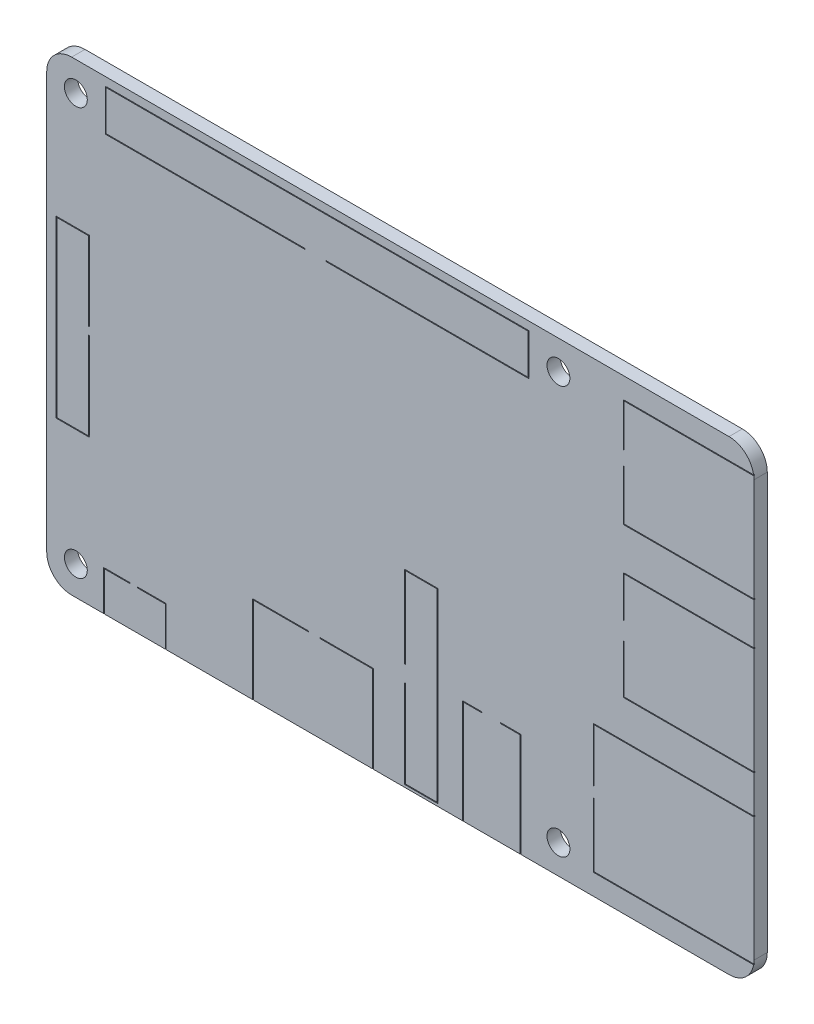
SolidWorks part; units mm, degrees
ref_plane "Front Plane" through (0, 0, 0) normal (0, 0, 1) x (1, 0, 0)
ref_plane "Top Plane" through (0, 0, 0) normal (0, 1, 0) x (1, 0, 0)
ref_plane "Right Plane" through (0, 0, 0) normal (1, 0, 0) x (0, 0, -1)
sketch "Sketch1" plane through (0, 0, 0) normal (0, 0, 1) x (1, 0, 0)
  line L1 (-39.5, -28) -> (39.5, -28)
  line L2 (-42.5, -25) -> (-42.5, 25)
  line L3 (-39.5, 28) -> (39.5, 28)
  line L4 (42.5, -25) -> (42.5, 25)
  line L5 (-42.5, -28) -> (42.5, 28) construction
  line L6 (-42.5, 28) -> (42.5, -28) construction
  arc A0 (-39.5, -28) -> (-42.5, -25) centre (-39.5, -25) cw
  arc A1 (39.5, -28) -> (42.5, -25) centre (39.5, -25) ccw
  arc A2 (39.5, 28) -> (42.5, 25) centre (39.5, 25) cw
  arc A3 (-42.5, 25) -> (-39.5, 28) centre (-39.5, 25) cw
  circle A4 centre (-39, 24.5) radius 1.375
  circle A5 centre (-39, -24.5) radius 1.375
  circle A6 centre (19, 24.5) radius 1.375
  circle A7 centre (19, -24.5) radius 1.375
  point P0 (0, 0)
  dimension "D3" = 3
  dimension "D4" = 2.75
  dimension "D5" = 3.5
  dimension "D6" = 3.5
  dimension "D7" = 58
  dimension "D8" = 58
  dimension "D9" = 49
  dimension "D12" = 49
  dimension "D1" = 85
  dimension "D2" = 56
  dimension "D10" = 24.5
  dimension "D11" = 24.5
extrude "Boss-Extrude1" add sketch "Sketch1" along normal blind 1.6
sketch "Sketch2" plane through (0, 0, 1.6) normal (0, 0, 1) x (1, 0, 0)
  line L1 (-42.5, 25) -> (-42.5, -25) construction
  line L2 (-35.65, -28.6369) -> (-28.15, -28.6369)
  line L3 (-35.65, -28.6369) -> (-35.65, -23.2)
  line L4 (-35.65, -23.2) -> (-32.465, -23.2)
  line L5 (-28.15, -28.6369) -> (-28.15, -23.2)
  line L6 (-35.65, -28.6369) -> (-28.15, -23.2) construction
  line L7 (-35.65, -23.2) -> (-28.15, -28.6369) construction
  line L8 (-39.5, -28) -> (39.5, -28) construction
  line L9 (-17.75, -17.5) -> (-11.0158, -17.5)
  line L10 (-17.75, -17.5) -> (-17.75, -33.1614)
  line L11 (-17.75, -33.1614) -> (-3.25, -33.1614)
  line L12 (-3.25, -17.5) -> (-3.25, -33.1614)
  line L13 (-17.75, -17.5) -> (-3.25, -33.1614) construction
  line L14 (-17.75, -33.1614) -> (-3.25, -17.5) construction
  line L15 (0.5, -5.3) -> (4.5, -5.3)
  line L16 (0.5, -5.3) -> (0.5, -15.174)
  line L17 (0.5, -27.7) -> (4.5, -27.7)
  line L18 (4.5, -5.3) -> (4.5, -27.7)
  line L19 (0.5, -5.3) -> (4.5, -27.7) construction
  line L20 (0.5, -27.7) -> (4.5, -5.3) construction
  line L21 (7.5, -15.5) -> (9.7992, -15.5)
  line L22 (7.5, -15.5) -> (7.5, -31.1614)
  line L23 (7.5, -31.1614) -> (14.5, -31.1614)
  line L24 (14.5, -15.5) -> (14.5, -31.1614)
  line L25 (7.5, -15.5) -> (14.5, -31.1614) construction
  line L26 (7.5, -31.1614) -> (14.5, -15.5) construction
  line L27 (-35.45, 27) -> (15.45, 27)
  line L28 (-35.45, 27) -> (-35.45, 22)
  line L29 (-35.45, 22) -> (-11.4582, 22)
  line L30 (15.45, 27) -> (15.45, 22)
  line L31 (-35.45, 27) -> (15.45, 22) construction
  line L32 (-35.45, 22) -> (15.45, 27) construction
  line L33 (-41.3717, -10.5142) -> (-37.3717, -10.5142)
  line L34 (-41.3717, -10.5142) -> (-41.3717, 10.5142)
  line L35 (-41.3717, 10.5142) -> (-37.3717, 10.5142)
  line L36 (-37.3717, -10.5142) -> (-37.3717, 0.0947)
  line L37 (-41.3717, -10.5142) -> (-37.3717, 10.5142) construction
  line L38 (-41.3717, 10.5142) -> (-37.3717, -10.5142) construction
  line L39 (42.5, -25) -> (42.5, 25) construction
  line L40 (23.2, -25.5) -> (44.7, -25.5)
  line L41 (23.2, -25.5) -> (23.2, -17.75)
  line L42 (23.2, -10) -> (44.7, -10)
  line L43 (44.7, -25.5) -> (44.7, -10)
  line L44 (23.2, -25.5) -> (44.7, -10) construction
  line L45 (23.2, -10) -> (44.7, -25.5) construction
  line L46 (26.8, -5.5) -> (54.0714, -5.5)
  line L47 (26.8, -5.5) -> (26.8, 0.4072)
  line L48 (26.8, 7.5) -> (54.0714, 7.5)
  line L49 (54.0714, -5.5) -> (54.0714, 7.5)
  line L50 (26.8, -5.5) -> (54.0714, 7.5) construction
  line L51 (26.8, 7.5) -> (54.0714, -5.5) construction
  line L52 (26.8, 12.5) -> (57.7137, 12.5)
  line L53 (26.8, 12.5) -> (26.8, 18.6113)
  line L54 (26.8, 25.5) -> (57.7137, 25.5)
  line L55 (57.7137, 12.5) -> (57.7137, 25.5)
  line L56 (26.8, 12.5) -> (57.7137, 25.5) construction
  line L57 (26.8, 25.5) -> (57.7137, 12.5) construction
  line L58 (-35.35, 22.1) -> (-11.4582, 22.1)
  line L59 (15.35, 26.9) -> (15.35, 22.1)
  line L60 (-35.35, 26.9) -> (15.35, 26.9)
  line L61 (-35.35, 26.9) -> (-35.35, 22.1)
  line L62 (-41.2717, 10.4142) -> (-37.4717, 10.4142)
  line L63 (-37.4717, -10.4142) -> (-37.4717, 0.0947)
  line L64 (-41.2717, -10.4142) -> (-37.4717, -10.4142)
  line L65 (-41.2717, -10.4142) -> (-41.2717, 10.4142)
  line L66 (-35.55, -28.5369) -> (-35.55, -23.3)
  line L67 (-35.55, -23.3) -> (-32.465, -23.3)
  line L68 (-28.25, -28.5369) -> (-28.25, -23.3)
  line L69 (-35.55, -28.5369) -> (-28.25, -28.5369)
  line L70 (-17.65, -17.6) -> (-17.65, -33.0614)
  line L71 (-17.65, -33.0614) -> (-3.35, -33.0614)
  line L72 (-3.35, -17.6) -> (-3.35, -33.0614)
  line L73 (-17.65, -17.6) -> (-11.0158, -17.6)
  line L74 (0.6, -5.4) -> (0.6, -15.174)
  line L75 (0.6, -27.6) -> (4.4, -27.6)
  line L76 (4.4, -5.4) -> (4.4, -27.6)
  line L77 (0.6, -5.4) -> (4.4, -5.4)
  line L78 (7.6, -15.6) -> (9.7992, -15.6)
  line L79 (14.4, -15.6) -> (14.4, -31.0614)
  line L80 (7.6, -31.0614) -> (14.4, -31.0614)
  line L81 (7.6, -15.6) -> (7.6, -31.0614)
  line L82 (23.3, -25.4) -> (23.3, -17.75)
  line L83 (23.3, -10.1) -> (44.6, -10.1)
  line L84 (44.6, -25.4) -> (44.6, -10.1)
  line L85 (23.3, -25.4) -> (44.6, -25.4)
  line L86 (26.9, -5.4) -> (53.9714, -5.4)
  line L87 (53.9714, -5.4) -> (53.9714, 7.4)
  line L88 (26.9, 7.4) -> (53.9714, 7.4)
  line L89 (26.9, -5.4) -> (26.9, 0.4072)
  line L90 (26.9, 12.6) -> (57.6137, 12.6)
  line L91 (57.6137, 12.6) -> (57.6137, 25.4)
  line L92 (26.9, 25.4) -> (57.6137, 25.4)
  line L93 (26.9, 12.6) -> (26.9, 18.6113)
  line L94 (-37.4717, 1) -> (-37.4717, 10.4142)
  line L95 (-37.4717, 1) -> (-37.3717, 1)
  line L96 (26.9, 20.2773) -> (26.9, 25.4)
  line L97 (-37.4717, 0.0947) -> (-37.3717, 0.0947)
  line L98 (26.9, 12.6) -> (26.9, 25.4) construction
  line L99 (-37.4717, -10.4142) -> (-37.4717, 10.4142) construction
  line L100 (-37.3717, 1) -> (-37.3717, 10.5142)
  line L101 (-37.3717, -10.5142) -> (-37.3717, 10.5142) construction
  line L102 (26.8, 20.2773) -> (26.9, 20.2773)
  line L103 (26.9, 2.5528) -> (26.9, 7.4)
  line L104 (26.8, 18.6113) -> (26.9, 18.6113)
  line L105 (26.9, -5.4) -> (26.9, 7.4) construction
  line L106 (26.8, 20.2773) -> (26.8, 25.5)
  line L107 (26.8, 12.5) -> (26.8, 25.5) construction
  line L108 (23.2, -16.5) -> (23.3, -16.5)
  line L109 (12.0626, -15.5) -> (14.5, -15.5)
  line L110 (23.2, -17.75) -> (23.3, -17.75)
  line L111 (7.5, -15.5) -> (14.5, -15.5) construction
  line L112 (26.8, 2.5528) -> (26.9, 2.5528)
  line L113 (23.2, -16.5) -> (23.2, -10)
  line L114 (26.8, 0.4072) -> (26.9, 0.4072)
  line L115 (23.2, -25.5) -> (23.2, -10) construction
  line L116 (-8.9067, 22.1) -> (15.35, 22.1)
  line L117 (-32.465, -23.2) -> (-32.465, -23.3)
  line L118 (-35.35, 22.1) -> (15.35, 22.1) construction
  line L119 (-31.5737, -23.2) -> (-31.5737, -23.3)
  line L120 (-31.5737, -23.3) -> (-28.25, -23.3)
  line L121 (-11.0158, -17.5) -> (-11.0158, -17.6)
  line L122 (-35.55, -23.3) -> (-28.25, -23.3) construction
  line L123 (-9.6849, -17.5) -> (-9.6849, -17.6)
  line L124 (0.5, -15.174) -> (0.6, -15.174)
  line L125 (-9.6849, -17.5) -> (-3.25, -17.5)
  line L126 (0.5, -17.125) -> (0.6, -17.125)
  line L127 (-17.75, -17.5) -> (-3.25, -17.5) construction
  line L128 (0.5, -17.125) -> (0.5, -27.7)
  line L129 (9.7992, -15.5) -> (9.7992, -15.6)
  line L130 (0.5, -5.3) -> (0.5, -27.7) construction
  line L131 (12.0626, -15.5) -> (12.0626, -15.6)
  line L132 (26.8, 2.5528) -> (26.8, 7.5)
  line L133 (26.8, -5.5) -> (26.8, 7.5) construction
  line L134 (23.3, -16.5) -> (23.3, -10.1)
  line L135 (23.3, -25.4) -> (23.3, -10.1) construction
  line L136 (12.0626, -15.6) -> (14.4, -15.6)
  line L137 (7.6, -15.6) -> (14.4, -15.6) construction
  line L138 (0.6, -17.125) -> (0.6, -27.6)
  line L139 (0.6, -5.4) -> (0.6, -27.6) construction
  line L140 (-9.6849, -17.6) -> (-3.35, -17.6)
  line L141 (-17.65, -17.6) -> (-3.35, -17.6) construction
  line L142 (-31.5737, -23.2) -> (-28.15, -23.2)
  line L143 (-35.65, -23.2) -> (-28.15, -23.2) construction
  line L145 (-11.4582, 22.1) -> (-11.4582, 22)
  line L147 (-8.9067, 22.1) -> (-8.9067, 22)
  line L148 (-8.9067, 22) -> (15.45, 22)
  line L149 (-35.45, 22) -> (15.45, 22) construction
  circle A0 centre (-39, 24.5) radius 1.375 construction
  point P0 (-31.9, -25.9184)
  point P7 (-10.5, -25.3307)
  point P12 (2.5, -16.5)
  point P17 (11, -23.3307)
  point P22 (-10, 24.5)
  point P29 (-39.3717, 0)
  point P36 (33.95, -17.75)
  point P41 (40.4357, 1)
  point P46 (42.2569, 19)
  dimension "D5" = 29
  dimension "D26" = 0
  dimension "D1" = 10.6
  dimension "D2" = 32
  dimension "D3" = 13
  dimension "D4" = 53.5
  dimension "D6" = 28
  dimension "D7" = 11.5
  dimension "D8" = 10.25
  dimension "D9" = 29
  dimension "D10" = 47
  dimension "D11" = 7.5
  dimension "D12" = 4.8
  dimension "D13" = 14.5
  dimension "D14" = 10.5
  dimension "D15" = 4
  dimension "D16" = 22.7
  dimension "D17" = 7
  dimension "D18" = 12.5
  dimension "D19" = 15.5
  dimension "D20" = 19.3
  dimension "D21" = 21.5
  dimension "D22" = 13
  dimension "D23" = 13
  dimension "D24" = 15.7
  dimension "D25" = 15.7
  dimension "D27" = 5
  dimension "D28" = 50.9
  dimension "D29" = 4
  dimension "D30" = 0.1
extrude "Cut-Extrude1" cut sketch "Sketch2" against normal blind 0.1
